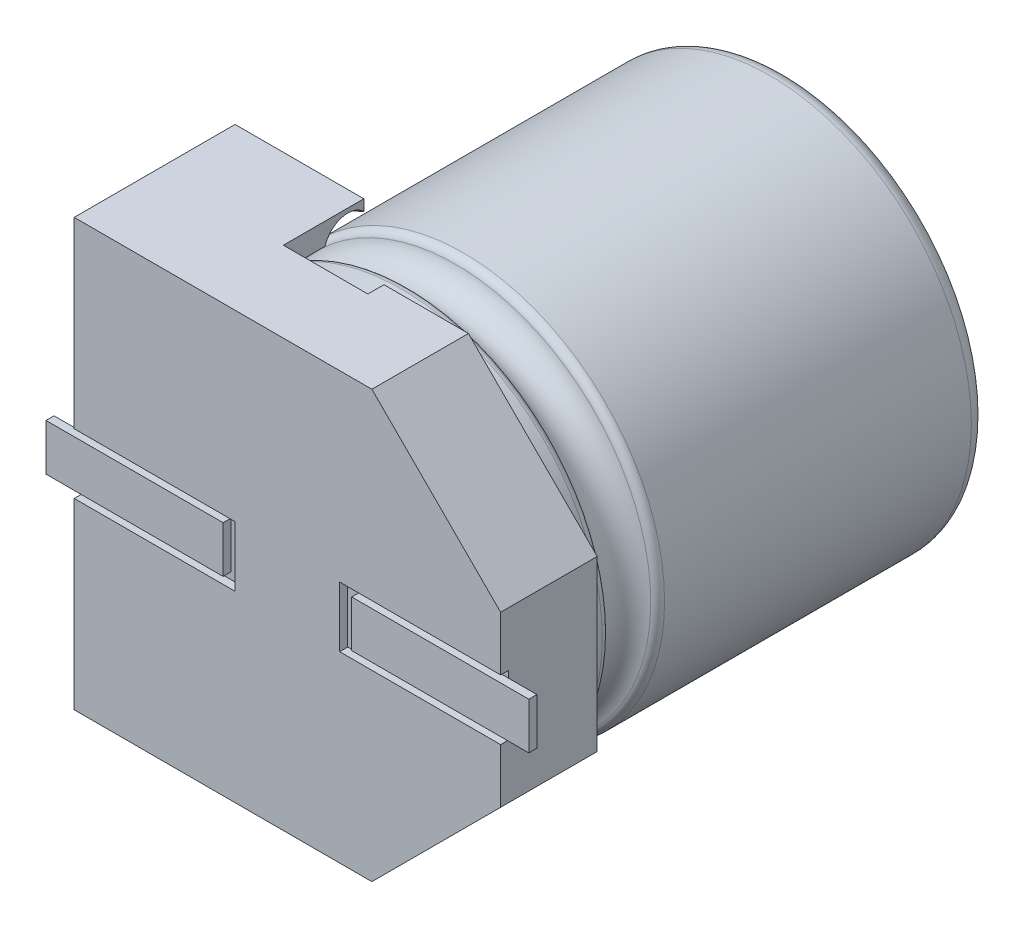
SolidWorks part; units mm, degrees
ref_plane "Front Plane" through (0, 0, 0) normal (0, 0, 1) x (1, 0, 0)
ref_plane "Top Plane" through (0, 0, 0) normal (0, 1, 0) x (1, 0, 0)
ref_plane "Right Plane" through (0, 0, 0) normal (1, 0, 0) x (0, 0, -1)
sketch "Szkic1" plane through (0, 0, 0) normal (0, 0, 1) x (1, 0, 0)
  line L0 (2.65, -1.05) -> (2.65, -0.375)
  line L1 (2.65, -0.375) -> (0.65, -0.375)
  line L2 (0.65, -0.375) -> (0.65, 0.375)
  line L3 (0.65, 0.375) -> (2.65, 0.375)
  line L4 (2.65, 0.375) -> (2.65, 1.05)
  line L5 (2.65, 1.05) -> (1.05, 2.65)
  line L6 (1.05, 2.65) -> (-2.65, 2.65)
  line L7 (-2.65, 2.65) -> (-2.65, 0.375)
  line L8 (-2.65, 0.375) -> (-0.65, 0.375)
  line L9 (-0.65, 0.375) -> (-0.65, -0.375)
  line L10 (-0.65, -0.375) -> (-2.65, -0.375)
  line L11 (-2.65, -0.375) -> (-2.65, -2.65)
  line L12 (-2.65, -2.65) -> (1.05, -2.65)
  line L13 (1.05, -2.65) -> (2.65, -1.05)
extrude "Dodanie-wyciągnięcie1" add sketch "Szkic1" along normal blind 2
sketch "Szkic2" plane through (0, 0, 0) normal (0, 0, -1) x (-1, 0, 0)
  line L0 (-2.65, 0.375) -> (-0.65, 0.375)
  line L1 (-0.65, 0.375) -> (-0.65, -0.375)
  line L2 (-0.65, -0.375) -> (-2.65, -0.375)
  line L3 (-2.65, -0.375) -> (-2.65, 0.375)
  line L4 (0.65, 0.375) -> (0.65, -0.375)
  line L5 (0.65, -0.375) -> (2.65, -0.375)
  line L6 (2.65, -0.375) -> (2.65, 0.375)
  line L7 (2.65, 0.375) -> (0.65, 0.375) construction
  line L8 (2.65, 0.375) -> (0.65, 0.375)
extrude "Dodanie-wyciągnięcie2" add sketch "Szkic2" against normal blind 1.9
sketch "Szkic3" plane through (0, 0, 1.9) normal (0, 0, 1) x (1, 0, 0)
  line L0 (0.65, 0) -> (-0.65, 0) construction
  line L1 (0.65, -0.375) -> (0.65, 0.375) construction
  line L2 (-0.65, 0.375) -> (-0.65, -0.375) construction
  line L3 (0, 0) -> (0, -0.9465) construction
  line L4 (3, 0.289) -> (0.7996, 0.289)
  line L5 (0.7996, 0.289) -> (0.7996, -0.289)
  line L6 (0.7996, -0.289) -> (3, -0.289)
  line L7 (3, -0.289) -> (3, 0.289)
  line L8 (2.65, -1.05) -> (2.65, -0.375) construction
  line L9 (-3, -0.289) -> (-3, 0.289)
  line L10 (-0.7996, -0.289) -> (-3, -0.289)
  line L11 (-0.7996, 0.289) -> (-0.7996, -0.289)
  line L12 (-3, 0.289) -> (-0.7996, 0.289)
  dimension "D1" = 0.35
extrude "Dodanie-wyciągnięcie3" add sketch "Szkic3" along normal blind 0.1 separate body
sketch "Szkic4" plane through (0, 0, 0) normal (0, 0, -1) x (-1, 0, 0)
  line L0 (1.05, 2.65) -> (0, 2.65)
  line L1 (0, 2.65) -> (0, 2.6)
  line L2 (0, -2.6) -> (0, -2.65)
  line L3 (0, -2.65) -> (1.05, -2.65)
  line L4 (1.05, -2.65) -> (1.05, -2.3785)
  line L5 (2.3785, -1.05) -> (2.65, -1.05)
  line L6 (2.65, -1.05) -> (2.65, 1.05)
  line L7 (2.65, 1.05) -> (2.3785, 1.05)
  line L8 (1.05, 2.3785) -> (1.05, 2.65)
  line L9 (2.65, 2.65) -> (2.65, -2.65) construction
  arc A0 (0, 2.6) -> (0, -2.6) centre (0, 0) ccw
  arc A1 (1.05, -2.3785) -> (2.3785, -1.05) centre (0, 0) ccw
  arc A2 (2.3785, 1.05) -> (1.05, 2.3785) centre (0, 0) ccw
  point P15 (2.65, 0)
  point P16 (2.65, 0)
extrude "Wytnij-wyciągnięcie1" cut sketch "Szkic4" against normal blind 1
sketch "Szkic5" plane through (0, 0, 0) normal (0, 0, -1) x (-1, 0, 0)
  line L0 (0.4947, 3.838) -> (0.4947, -3.9403)
  line L1 (0.4947, -3.9403) -> (-3.5992, -3.3262)
  line L2 (-3.5992, -3.3262) -> (-6.2261, 2.1322)
  line L3 (-6.2261, 2.1322) -> (0.4947, 3.838)
extrude "Wytnij-wyciągnięcie2" cut sketch "Szkic5" against normal blind 0.8
sketch "Szkic6" plane through (0, 0, 1) normal (0, 0, -1) x (-1, 0, 0)
  circle A0 centre (0, 0) radius 2.5
  dimension "D1" = 5
extrude "Dodanie-wyciągnięcie4" add sketch "Szkic6" along normal blind 5.2 separate body
fillet "Zaokrąglenie1" radius 0.2 1 edges at (-2.5, 0, -4.2)
sketch "Szkic7" plane through (0, 0, -4.2) normal (0, 0, -1) x (-1, 0, 0)
  line L0 (0.619, -2.2151) -> (0.6188, 2.2152)
  line L1 (0.6188, 2.2152) -> (0.619, -2.2151)
  circle A4 centre (0, 0) radius 2.3 construction
sketch "Szkic8" plane through (0, 0, -4.2) normal (0, 0, -1) x (-1, 0, 0)
  line L0 (-2.0064, -1.1245) -> (2.0064, -1.1245)
  line L1 (0, 0) -> (-2.3, 0) construction
  circle A0 centre (0, 0) radius 2.3 construction
split line "Linia podziałowa4"
sketch "Szkic9" plane through (0, 0, 0) normal (0, 1, 0) x (1, 0, 0)
  line L0 (2.5, -1) -> (2.5, -0.2) construction
  line L1 (2.6, -1) -> (0, -1) construction
  line L2 (-2.5, -1) -> (2.5, -1) construction
  circle A0 centre (2.5, -0.2) radius 0.3
  dimension "D2" = 0.6
  dimension "D1" = 0.8
revolve "Wycięcie-obrót1" cut sketch "Szkic9" angle 360 about axis through (0, 0, -4.2) along (0, 0, 1)
fillet "Zaokrąglenie2" radius 0.1 2 edges at (-2.5, 0, 0.5) (2.5, 0, -0.1)
sketch "Szkic10" plane through (0, 0, -4.2) normal (0, 0, -1) x (-1, 0, 0)
  line L0 (-1.1, -1.1245) -> (-1.1, 1.5549) construction
  line L1 (2.0064, -1.1245) -> (-2.0064, -1.1245) construction
  line L2 (0, -1.1245) -> (0, 1.5549) construction
  line L3 (1.1, -1.1245) -> (1.1, 1.5549) construction
  text T0 "CS" font "Century Gothic" height 1
  text T1 "47" font "Century Gothic" height 1
  text T2 "25V" font "Century Gothic" height 1
  dimension "D1" = 1.1
  dimension "D2" = 1.1
split line "Linia podziałowa5"
